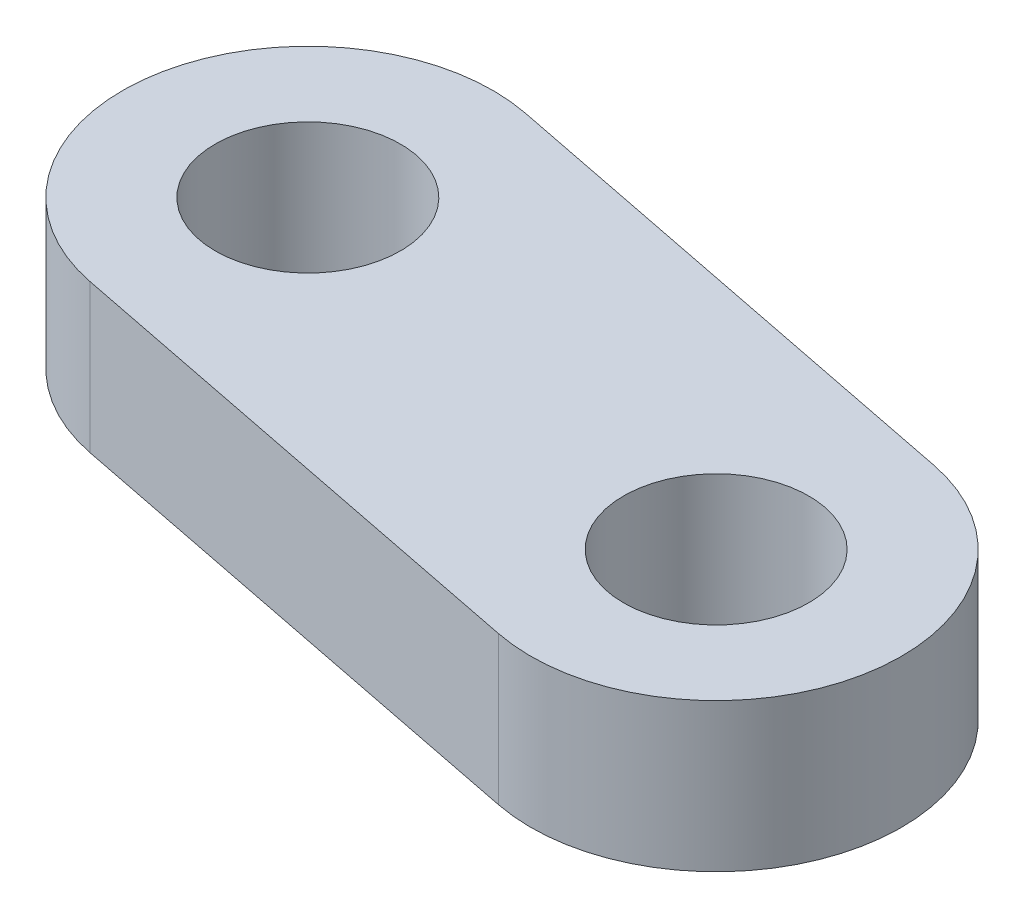
SolidWorks part; units mm, degrees
ref_plane "Alzado" through (0, 0, 0) normal (0, 0, 1) x (1, 0, 0)
ref_plane "Planta" through (0, 0, 0) normal (0, 1, 0) x (1, 0, 0)
ref_plane "Vista lateral" through (0, 0, 0) normal (1, 0, 0) x (0, 0, -1)
sketch "Croquis1" plane through (0, 0, 0) normal (0, 1, 0) x (1, 0, 0)
  line L1 (24.5208, -25) -> (-25.4792, -25)
  line L2 (24.5208, -25) -> (24.5208, 25)
  line L4 (-25.4792, -25) -> (-25.4792, 25)
  circle A0 centre (-0.4792, 20.0815) radius 12.5
  arc A1 (24.5208, 25) -> (-25.4792, 25) centre (-0.4792, 20.0815) ccw
  point P0 (0, 0)
  dimension "D5" = 25
  dimension "D1" = 50
  dimension "D2" = 50
  dimension "D3" = 50
  dimension "D4" = 25
extrude "Saliente-Extruir1" [suppressed] add sketch "Croquis1" along normal blind 20
sketch "Croquis2" plane through (0, 0, 0) normal (0, 1, 0) x (1, 0, 0)
  circle A0 centre (0, 0) radius 12.5
  dimension "D1" = 25
extrude "Saliente-Extruir2" [suppressed] add sketch "Croquis2" along normal blind 35
sketch "Croquis3" plane through (0, 0, 0) normal (0, 1, 0) x (1, 0, 0)
  line L0 (0, 0) -> (68.671, -13.5753) construction
  line L1 (4.8483, 24.5254) -> (73.5194, 10.9501)
  line L2 (-4.8483, -24.5254) -> (63.8227, -38.1006)
  arc A0 (4.8483, 24.5254) -> (-4.8483, -24.5254) centre (0, 0) ccw
  arc A1 (63.8227, -38.1006) -> (73.5194, 10.9501) centre (68.671, -13.5753) ccw
  circle A2 centre (0, 0) radius 12.5
  circle A3 centre (68.671, -13.5753) radius 12.5
  point P3 (34.3355, -6.7876)
  dimension "D2" = 25
  dimension "D3" = 25
  dimension "D4" = 25
  dimension "D1" = 70
extrude "Saliente-Extruir3" add sketch "Croquis3" along normal blind 20
